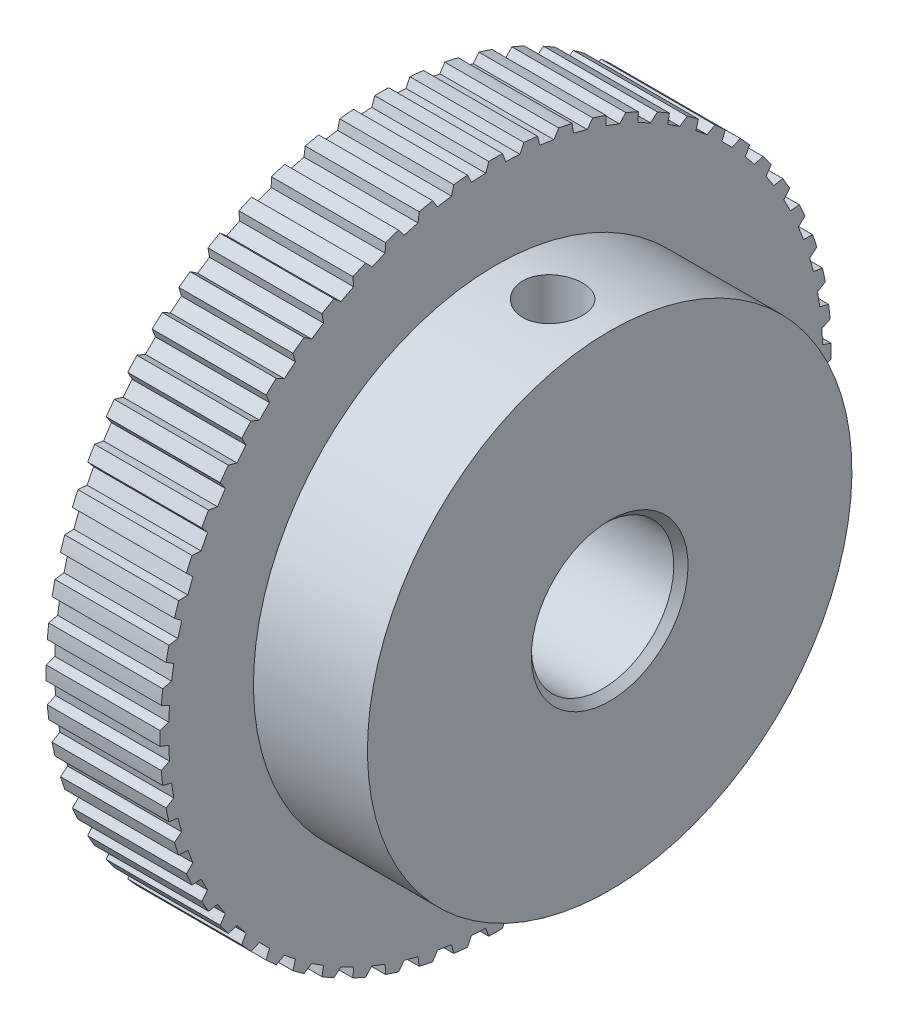
SolidWorks part; units mm, degrees
material "3.1325 (EN-AW 2017A)"
ref_plane "Plan de face" through (0, 0, 0) normal (0, 0, 1) x (1, 0, 0)
ref_plane "Plan de dessus" through (0, 0, 0) normal (0, 1, 0) x (1, 0, 0)
ref_plane "Plan de droite" through (0, 0, 0) normal (1, 0, 0) x (0, 0, -1)
sketch "Esquisse1" plane through (0, 0, 0) normal (0, 0, 1) x (1, 0, 0)
  line L0 (0, 0) -> (0, 21.05)
  line L1 (0, 23.55) -> (8, 23.55)
  line L2 (8, 21.05) -> (8, 17)
  line L3 (8, 17) -> (16, 17)
  line L4 (16, 17) -> (16, 0)
  line L5 (16, 0) -> (0, 0)
  line L7 (8, 23.55) -> (8, 21.05)
  line L11 (0, 23.55) -> (0, 21.05)
  dimension "D2" = 17
  dimension "D3" = 16
revolve "Révolution1" add sketch "Esquisse1" angle 360 about L5
sketch "Esquisse2" plane through (0, 0, 0) normal (-1, 0, 0) x (0, 0, 1)
  line L0 (0.7011, 22.9448) -> (0.419, 23.7199)
  line L1 (0.7011, 22.9448) -> (1.7011, 22.8923)
  line L2 (3.0956, 22.7458) -> (2.8961, 23.5462)
  line L3 (2.8961, 23.5462) -> (4.5218, 23.2887)
  line L4 (4.0847, 22.5891) -> (4.5218, 23.2887)
  line L5 (1.7011, 22.8923) -> (2.0627, 23.6338)
  line L6 (0.419, 23.7199) -> (2.0627, 23.6338)
  line L7 (3.0956, 22.7458) -> (4.0847, 22.5891)
  line L8 (5.4563, 22.2976) -> (5.3415, 23.1145)
  line L9 (5.3415, 23.1145) -> (6.9314, 22.6885)
  line L10 (6.4235, 22.0384) -> (6.9314, 22.6885)
  line L11 (5.4563, 22.2976) -> (6.4235, 22.0384)
  line L12 (7.7571, 21.6051) -> (7.7283, 22.4295)
  line L13 (7.7283, 22.4295) -> (9.265, 21.8396)
  line L14 (8.692, 21.2462) -> (9.265, 21.8396)
  line L15 (7.7571, 21.6051) -> (8.692, 21.2462)
  line L16 (9.973, 20.6759) -> (10.0305, 21.4988)
  line L17 (10.0305, 21.4988) -> (11.4971, 20.7515)
  line L18 (10.8652, 20.2213) -> (11.4971, 20.7515)
  line L19 (9.973, 20.6759) -> (10.8652, 20.2213)
  line L20 (12.0796, 19.5202) -> (12.2228, 20.3326)
  line L21 (12.2228, 20.3326) -> (13.6033, 19.4361)
  line L22 (12.9194, 18.9748) -> (13.6033, 19.4361)
  line L23 (12.0796, 19.5202) -> (12.9194, 18.9748)
  line L24 (14.0538, 18.1506) -> (14.2812, 18.9435)
  line L25 (14.2812, 18.9435) -> (15.5604, 17.9077)
  line L26 (14.832, 17.5204) -> (15.5604, 17.9077)
  line L27 (14.0538, 18.1506) -> (14.832, 17.5204)
  line L28 (15.8741, 16.5821) -> (16.1831, 17.347)
  line L29 (16.1831, 17.347) -> (17.347, 16.1831)
  line L30 (16.5821, 15.8741) -> (17.347, 16.1831)
  line L31 (15.8741, 16.5821) -> (16.5821, 15.8741)
  line L32 (17.5204, 14.832) -> (17.9077, 15.5604)
  line L33 (17.9077, 15.5604) -> (18.9435, 14.2812)
  line L34 (18.1506, 14.0538) -> (18.9435, 14.2812)
  line L35 (17.5204, 14.832) -> (18.1506, 14.0538)
  line L36 (18.9748, 12.9194) -> (19.4361, 13.6033)
  line L37 (19.4361, 13.6033) -> (20.3326, 12.2228)
  line L38 (19.5202, 12.0796) -> (20.3326, 12.2228)
  line L39 (18.9748, 12.9194) -> (19.5202, 12.0796)
  line L40 (20.2213, 10.8652) -> (20.7515, 11.4971)
  line L41 (20.7515, 11.4971) -> (21.4988, 10.0305)
  line L42 (20.6759, 9.973) -> (21.4988, 10.0305)
  line L43 (20.2213, 10.8652) -> (20.6759, 9.973)
  line L44 (21.2462, 8.692) -> (21.8396, 9.265)
  line L45 (21.8396, 9.265) -> (22.4295, 7.7283)
  line L46 (21.6051, 7.7571) -> (22.4295, 7.7283)
  line L47 (21.2462, 8.692) -> (21.6051, 7.7571)
  line L48 (22.0384, 6.4235) -> (22.6885, 6.9314)
  line L49 (22.6885, 6.9314) -> (23.1145, 5.3415)
  line L50 (22.2976, 5.4563) -> (23.1145, 5.3415)
  line L51 (22.0384, 6.4235) -> (22.2976, 5.4563)
  line L52 (22.5891, 4.0847) -> (23.2887, 4.5218)
  line L53 (23.2887, 4.5218) -> (23.5462, 2.8961)
  line L54 (22.7458, 3.0956) -> (23.5462, 2.8961)
  line L55 (22.5891, 4.0847) -> (22.7458, 3.0956)
  line L56 (22.8923, 1.7011) -> (23.6338, 2.0627)
  line L57 (23.6338, 2.0627) -> (23.7199, 0.419)
  line L58 (22.9448, 0.7011) -> (23.7199, 0.419)
  line L59 (22.8923, 1.7011) -> (22.9448, 0.7011)
  line L60 (22.9448, -0.7011) -> (23.7199, -0.419)
  line L61 (23.7199, -0.419) -> (23.6338, -2.0627)
  line L62 (22.8923, -1.7011) -> (23.6338, -2.0627)
  line L63 (22.9448, -0.7011) -> (22.8923, -1.7011)
  line L64 (22.7458, -3.0956) -> (23.5462, -2.8961)
  line L65 (23.5462, -2.8961) -> (23.2887, -4.5218)
  line L66 (22.5891, -4.0847) -> (23.2887, -4.5218)
  line L67 (22.7458, -3.0956) -> (22.5891, -4.0847)
  line L68 (22.2976, -5.4563) -> (23.1145, -5.3415)
  line L69 (23.1145, -5.3415) -> (22.6885, -6.9314)
  line L70 (22.0384, -6.4235) -> (22.6885, -6.9314)
  line L71 (22.2976, -5.4563) -> (22.0384, -6.4235)
  line L72 (21.6051, -7.7571) -> (22.4295, -7.7283)
  line L73 (22.4295, -7.7283) -> (21.8396, -9.265)
  line L74 (21.2462, -8.692) -> (21.8396, -9.265)
  line L75 (21.6051, -7.7571) -> (21.2462, -8.692)
  line L76 (20.6759, -9.973) -> (21.4988, -10.0305)
  line L77 (21.4988, -10.0305) -> (20.7515, -11.4971)
  line L78 (20.2213, -10.8652) -> (20.7515, -11.4971)
  line L79 (20.6759, -9.973) -> (20.2213, -10.8652)
  line L80 (19.5202, -12.0796) -> (20.3326, -12.2228)
  line L81 (20.3326, -12.2228) -> (19.4361, -13.6033)
  line L82 (18.9748, -12.9194) -> (19.4361, -13.6033)
  line L83 (19.5202, -12.0796) -> (18.9748, -12.9194)
  line L84 (18.1506, -14.0538) -> (18.9435, -14.2812)
  line L85 (18.9435, -14.2812) -> (17.9077, -15.5604)
  line L86 (17.5204, -14.832) -> (17.9077, -15.5604)
  line L87 (18.1506, -14.0538) -> (17.5204, -14.832)
  line L88 (16.5821, -15.8741) -> (17.347, -16.1831)
  line L89 (17.347, -16.1831) -> (16.1831, -17.347)
  line L90 (15.8741, -16.5821) -> (16.1831, -17.347)
  line L91 (16.5821, -15.8741) -> (15.8741, -16.5821)
  line L92 (14.832, -17.5204) -> (15.5604, -17.9077)
  line L93 (15.5604, -17.9077) -> (14.2812, -18.9435)
  line L94 (14.0538, -18.1506) -> (14.2812, -18.9435)
  line L95 (14.832, -17.5204) -> (14.0538, -18.1506)
  line L96 (12.9194, -18.9748) -> (13.6033, -19.4361)
  line L97 (13.6033, -19.4361) -> (12.2228, -20.3326)
  line L98 (12.0796, -19.5202) -> (12.2228, -20.3326)
  line L99 (12.9194, -18.9748) -> (12.0796, -19.5202)
  line L100 (10.8652, -20.2213) -> (11.4971, -20.7515)
  line L101 (11.4971, -20.7515) -> (10.0305, -21.4988)
  line L102 (9.973, -20.6759) -> (10.0305, -21.4988)
  line L103 (10.8652, -20.2213) -> (9.973, -20.6759)
  line L104 (8.692, -21.2462) -> (9.265, -21.8396)
  line L105 (9.265, -21.8396) -> (7.7283, -22.4295)
  line L106 (7.7571, -21.6051) -> (7.7283, -22.4295)
  line L107 (8.692, -21.2462) -> (7.7571, -21.6051)
  line L108 (6.4235, -22.0384) -> (6.9314, -22.6885)
  line L109 (6.9314, -22.6885) -> (5.3415, -23.1145)
  line L110 (5.4563, -22.2976) -> (5.3415, -23.1145)
  line L111 (6.4235, -22.0384) -> (5.4563, -22.2976)
  line L112 (4.0847, -22.5891) -> (4.5218, -23.2887)
  line L113 (4.5218, -23.2887) -> (2.8961, -23.5462)
  line L114 (3.0956, -22.7458) -> (2.8961, -23.5462)
  line L115 (4.0847, -22.5891) -> (3.0956, -22.7458)
  line L116 (1.7011, -22.8923) -> (2.0627, -23.6338)
  line L117 (2.0627, -23.6338) -> (0.419, -23.7199)
  line L118 (0.7011, -22.9448) -> (0.419, -23.7199)
  line L119 (1.7011, -22.8923) -> (0.7011, -22.9448)
  line L120 (-0.7011, -22.9448) -> (-0.419, -23.7199)
  line L121 (-0.419, -23.7199) -> (-2.0627, -23.6338)
  line L122 (-1.7011, -22.8923) -> (-2.0627, -23.6338)
  line L123 (-0.7011, -22.9448) -> (-1.7011, -22.8923)
  line L124 (-3.0956, -22.7458) -> (-2.8961, -23.5462)
  line L125 (-2.8961, -23.5462) -> (-4.5218, -23.2887)
  line L126 (-4.0847, -22.5891) -> (-4.5218, -23.2887)
  line L127 (-3.0956, -22.7458) -> (-4.0847, -22.5891)
  line L128 (-5.4563, -22.2976) -> (-5.3415, -23.1145)
  line L129 (-5.3415, -23.1145) -> (-6.9314, -22.6885)
  line L130 (-6.4235, -22.0384) -> (-6.9314, -22.6885)
  line L131 (-5.4563, -22.2976) -> (-6.4235, -22.0384)
  line L132 (-7.7571, -21.6051) -> (-7.7283, -22.4295)
  line L133 (-7.7283, -22.4295) -> (-9.265, -21.8396)
  line L134 (-8.692, -21.2462) -> (-9.265, -21.8396)
  line L135 (-7.7571, -21.6051) -> (-8.692, -21.2462)
  line L136 (-9.973, -20.6759) -> (-10.0305, -21.4988)
  line L137 (-10.0305, -21.4988) -> (-11.4971, -20.7515)
  line L138 (-10.8652, -20.2213) -> (-11.4971, -20.7515)
  line L139 (-9.973, -20.6759) -> (-10.8652, -20.2213)
  line L140 (-12.0796, -19.5202) -> (-12.2228, -20.3326)
  line L141 (-12.2228, -20.3326) -> (-13.6033, -19.4361)
  line L142 (-12.9194, -18.9748) -> (-13.6033, -19.4361)
  line L143 (-12.0796, -19.5202) -> (-12.9194, -18.9748)
  line L144 (-14.0538, -18.1506) -> (-14.2812, -18.9435)
  line L145 (-14.2812, -18.9435) -> (-15.5604, -17.9077)
  line L146 (-14.832, -17.5204) -> (-15.5604, -17.9077)
  line L147 (-14.0538, -18.1506) -> (-14.832, -17.5204)
  line L148 (-15.8741, -16.5821) -> (-16.1831, -17.347)
  line L149 (-16.1831, -17.347) -> (-17.347, -16.1831)
  line L150 (-16.5821, -15.8741) -> (-17.347, -16.1831)
  line L151 (-15.8741, -16.5821) -> (-16.5821, -15.8741)
  line L152 (-17.5204, -14.832) -> (-17.9077, -15.5604)
  line L153 (-17.9077, -15.5604) -> (-18.9435, -14.2812)
  line L154 (-18.1506, -14.0538) -> (-18.9435, -14.2812)
  line L155 (-17.5204, -14.832) -> (-18.1506, -14.0538)
  line L156 (-18.9748, -12.9194) -> (-19.4361, -13.6033)
  line L157 (-19.4361, -13.6033) -> (-20.3326, -12.2228)
  line L158 (-19.5202, -12.0796) -> (-20.3326, -12.2228)
  line L159 (-18.9748, -12.9194) -> (-19.5202, -12.0796)
  line L160 (-20.2213, -10.8652) -> (-20.7515, -11.4971)
  line L161 (-20.7515, -11.4971) -> (-21.4988, -10.0305)
  line L162 (-20.6759, -9.973) -> (-21.4988, -10.0305)
  line L163 (-20.2213, -10.8652) -> (-20.6759, -9.973)
  line L164 (-21.2462, -8.692) -> (-21.8396, -9.265)
  line L165 (-21.8396, -9.265) -> (-22.4295, -7.7283)
  line L166 (-21.6051, -7.7571) -> (-22.4295, -7.7283)
  line L167 (-21.2462, -8.692) -> (-21.6051, -7.7571)
  line L168 (-22.0384, -6.4235) -> (-22.6885, -6.9314)
  line L169 (-22.6885, -6.9314) -> (-23.1145, -5.3415)
  line L170 (-22.2976, -5.4563) -> (-23.1145, -5.3415)
  line L171 (-22.0384, -6.4235) -> (-22.2976, -5.4563)
  line L172 (-22.5891, -4.0847) -> (-23.2887, -4.5218)
  line L173 (-23.2887, -4.5218) -> (-23.5462, -2.8961)
  line L174 (-22.7458, -3.0956) -> (-23.5462, -2.8961)
  line L175 (-22.5891, -4.0847) -> (-22.7458, -3.0956)
  line L176 (-22.8923, -1.7011) -> (-23.6338, -2.0627)
  line L177 (-23.6338, -2.0627) -> (-23.7199, -0.419)
  line L178 (-22.9448, -0.7011) -> (-23.7199, -0.419)
  line L179 (-22.8923, -1.7011) -> (-22.9448, -0.7011)
  line L180 (-22.9448, 0.7011) -> (-23.7199, 0.419)
  line L181 (-23.7199, 0.419) -> (-23.6338, 2.0627)
  line L182 (-22.8923, 1.7011) -> (-23.6338, 2.0627)
  line L183 (-22.9448, 0.7011) -> (-22.8923, 1.7011)
  line L184 (-22.7458, 3.0956) -> (-23.5462, 2.8961)
  line L185 (-23.5462, 2.8961) -> (-23.2887, 4.5218)
  line L186 (-22.5891, 4.0847) -> (-23.2887, 4.5218)
  line L187 (-22.7458, 3.0956) -> (-22.5891, 4.0847)
  line L188 (-22.2976, 5.4563) -> (-23.1145, 5.3415)
  line L189 (-23.1145, 5.3415) -> (-22.6885, 6.9314)
  line L190 (-22.0384, 6.4235) -> (-22.6885, 6.9314)
  line L191 (-22.2976, 5.4563) -> (-22.0384, 6.4235)
  line L192 (-21.6051, 7.7571) -> (-22.4295, 7.7283)
  line L193 (-22.4295, 7.7283) -> (-21.8396, 9.265)
  line L194 (-21.2462, 8.692) -> (-21.8396, 9.265)
  line L195 (-21.6051, 7.7571) -> (-21.2462, 8.692)
  line L196 (-20.6759, 9.973) -> (-21.4988, 10.0305)
  line L197 (-21.4988, 10.0305) -> (-20.7515, 11.4971)
  line L198 (-20.2213, 10.8652) -> (-20.7515, 11.4971)
  line L199 (-20.6759, 9.973) -> (-20.2213, 10.8652)
  line L200 (-19.5202, 12.0796) -> (-20.3326, 12.2228)
  line L201 (-20.3326, 12.2228) -> (-19.4361, 13.6033)
  line L202 (-18.9748, 12.9194) -> (-19.4361, 13.6033)
  line L203 (-19.5202, 12.0796) -> (-18.9748, 12.9194)
  line L204 (-18.1506, 14.0538) -> (-18.9435, 14.2812)
  line L205 (-18.9435, 14.2812) -> (-17.9077, 15.5604)
  line L206 (-17.5204, 14.832) -> (-17.9077, 15.5604)
  line L207 (-18.1506, 14.0538) -> (-17.5204, 14.832)
  line L208 (-16.5821, 15.8741) -> (-17.347, 16.1831)
  line L209 (-17.347, 16.1831) -> (-16.1831, 17.347)
  line L210 (-15.8741, 16.5821) -> (-16.1831, 17.347)
  line L211 (-16.5821, 15.8741) -> (-15.8741, 16.5821)
  line L212 (-14.832, 17.5204) -> (-15.5604, 17.9077)
  line L213 (-15.5604, 17.9077) -> (-14.2812, 18.9435)
  line L214 (-14.0538, 18.1506) -> (-14.2812, 18.9435)
  line L215 (-14.832, 17.5204) -> (-14.0538, 18.1506)
  line L216 (-12.9194, 18.9748) -> (-13.6033, 19.4361)
  line L217 (-13.6033, 19.4361) -> (-12.2228, 20.3326)
  line L218 (-12.0796, 19.5202) -> (-12.2228, 20.3326)
  line L219 (-12.9194, 18.9748) -> (-12.0796, 19.5202)
  line L220 (-10.8652, 20.2213) -> (-11.4971, 20.7515)
  line L221 (-11.4971, 20.7515) -> (-10.0305, 21.4988)
  line L222 (-9.973, 20.6759) -> (-10.0305, 21.4988)
  line L223 (-10.8652, 20.2213) -> (-9.973, 20.6759)
  line L224 (-8.692, 21.2462) -> (-9.265, 21.8396)
  line L225 (-9.265, 21.8396) -> (-7.7283, 22.4295)
  line L226 (-7.7571, 21.6051) -> (-7.7283, 22.4295)
  line L227 (-8.692, 21.2462) -> (-7.7571, 21.6051)
  line L228 (-6.4235, 22.0384) -> (-6.9314, 22.6885)
  line L229 (-6.9314, 22.6885) -> (-5.3415, 23.1145)
  line L230 (-5.4563, 22.2976) -> (-5.3415, 23.1145)
  line L231 (-6.4235, 22.0384) -> (-5.4563, 22.2976)
  line L232 (-4.0847, 22.5891) -> (-4.5218, 23.2887)
  line L233 (-4.5218, 23.2887) -> (-2.8961, 23.5462)
  line L234 (-3.0956, 22.7458) -> (-2.8961, 23.5462)
  line L235 (-4.0847, 22.5891) -> (-3.0956, 22.7458)
  line L236 (-1.7011, 22.8923) -> (-2.0627, 23.6338)
  line L237 (-2.0627, 23.6338) -> (-0.419, 23.7199)
  line L238 (-0.7011, 22.9448) -> (-0.419, 23.7199)
  line L239 (-1.7011, 22.8923) -> (-0.7011, 22.9448)
  point P5 (1.2011, 22.9185)
  point P6 (1.2409, 23.6768)
  dimension "D1" = 60
  dimension "D2" = 0.5
extrude "Enlèv. mat.-Extru.2" cut sketch "Esquisse2" against normal through all
sketch "Esquisse3" plane through (16, 0, 0) normal (1, 0, 0) x (0, 0, -1)
  circle A0 centre (0, 0) radius 5
extrude "Enlèv. mat.-Extru.3" cut sketch "Esquisse3" against normal through all
chamfer "Chanfrein1" distance 0.5 angle 45 2 edges at (0, 5, 0) (16, 5, 0)
hole_wizard "Trou taraudé M51" positions "Esquisse5" profile "Esquisse4" tap size "M5" standard "ISO"
sketch "Esquisse5" plane through (0, 0, 0) normal (0, 1, 0) x (1, 0, 0)
  line L0 (16, -17) -> (16, 17) construction
  point P0 (12, 0)
  dimension "D1" = 4
sketch "Esquisse4" plane through (12, 0, 0) normal (1, 0, 0) x (0, 0, -1)
  line L0 (0, 0) -> (0, 23.55)
  line L1 (0, 23.55) -> (2.1, 23.55)
  line L2 (2.1, 23.55) -> (2.1, 0)
  line L5 (2.1, 0) -> (0, 0)
  line L11 (0, -6.35) -> (0, 107.95) construction
  dimension "Diamètre du trou pour taraudage jusqu'au prochain" = 4.2
  dimension "Profondeur du trou pour taraudage jusqu'au prochain" = 23.55
cosmetic thread "Filetage de perçage1" parameters "D2"=5
